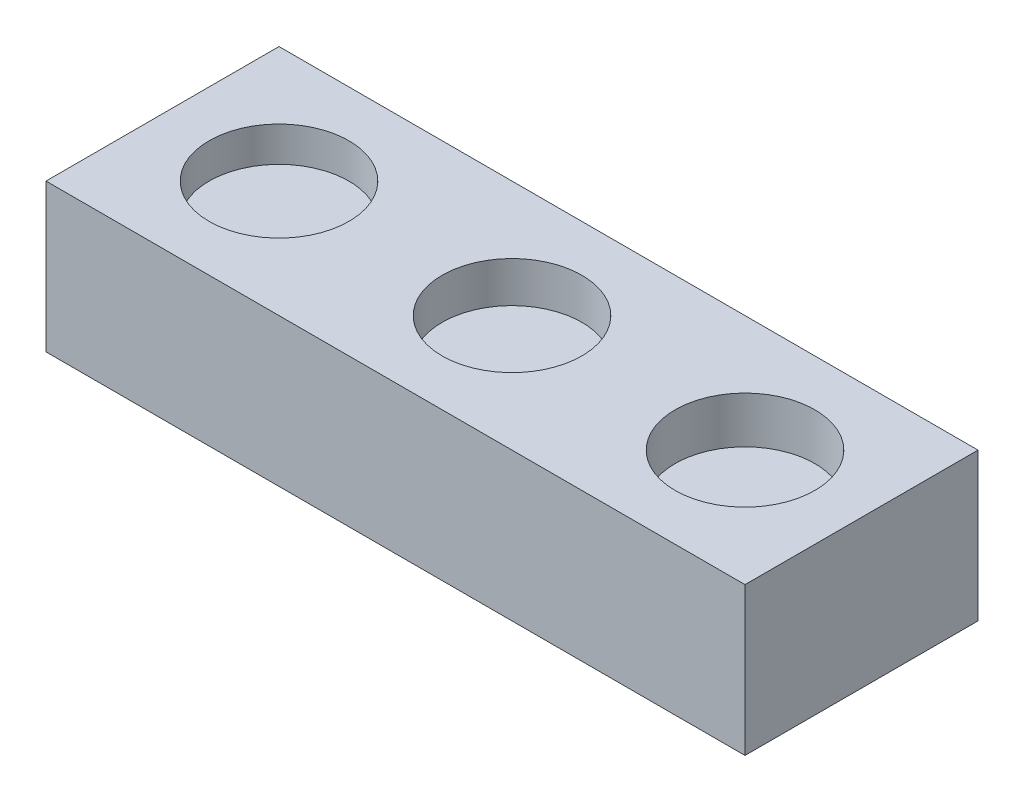
SolidWorks part; units mm, degrees
ref_plane "Front Plane" through (0, 0, 0) normal (0, 0, 1) x (1, 0, 0)
ref_plane "Top Plane" through (0, 0, 0) normal (0, 1, 0) x (1, 0, 0)
ref_plane "Right Plane" through (0, 0, 0) normal (1, 0, 0) x (0, 0, -1)
sketch "Sketch1" plane through (0, 0, 0) normal (0, 1, 0) x (1, 0, 0)
  line L1 (0, 0) -> (30, 0)
  line L2 (0, 0) -> (0, 10)
  line L3 (0, 10) -> (30, 10)
  line L4 (30, 0) -> (30, 10)
  dimension "D1" = 30
  dimension "D2" = 10
extrude "Boss-Extrude1" add sketch "Sketch1" along normal blind 6.35
sketch "Sketch2" plane through (0, 6.35, 0) normal (0, 1, 0) x (1, 0, 0)
  line L0 (30, 10) -> (0, 10) construction
  line L1 (30, 0) -> (30, 10) construction
  circle A0 centre (15, 5) radius 3
  point P4 (15, 10)
  point P7 (30, 5)
  point P10 (0, 0)
  dimension "D1" = 6
extrude "Cut-Extrude1" cut sketch "Sketch2" against normal blind 1.75
sketch "Sketch4" plane through (0, 6.35, 0) normal (0, 1, 0) x (1, 0, 0)
  line L0 (0, 10) -> (0, 0) construction
  circle A0 centre (5, 5) radius 3
  circle A1 centre (15, 5) radius 3 construction
  point P2 (0, 0)
  point P5 (0, 0)
  point P8 (0, 5)
  dimension "D1" = 10
extrude "Cut-Extrude2" cut sketch "Sketch4" against normal blind 1.5
sketch "Sketch5" plane through (0, 6.35, 0) normal (0, 1, 0) x (1, 0, 0)
  line L0 (0, 10) -> (0, 0) construction
  circle A0 centre (25, 5) radius 3
  circle A1 centre (15, 5) radius 3 construction
  point P2 (0, 0)
  point P5 (0, 0)
  point P8 (0, 5)
  dimension "D1" = 10
extrude "Cut-Extrude3" cut sketch "Sketch5" against normal blind 2
